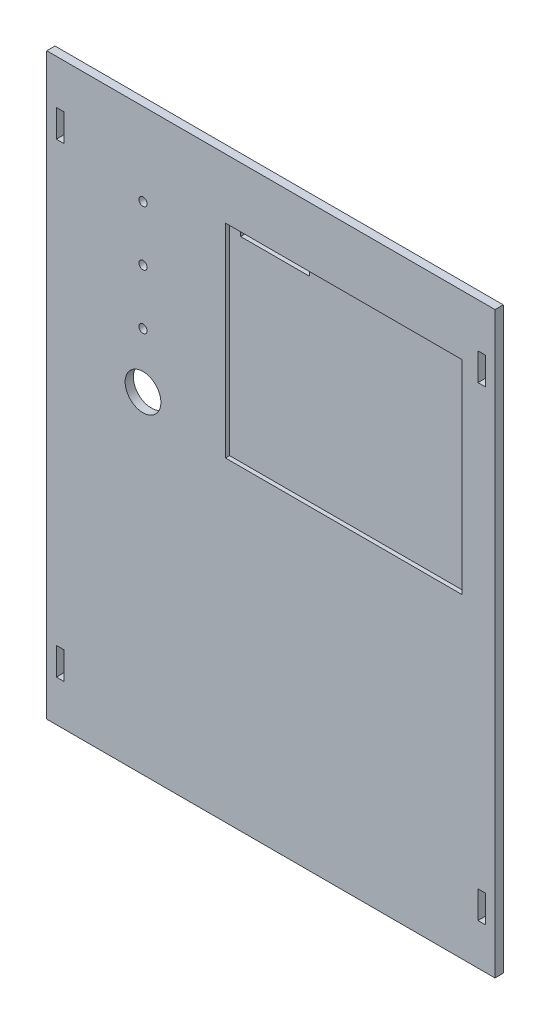
SolidWorks part; units mm, degrees
ref_plane "Front" through (0, 0, 0) normal (0, 0, 1) x (1, 0, 0)
ref_plane "Top" through (0, 0, 0) normal (0, 1, 0) x (1, 0, 0)
ref_plane "Right" through (0, 0, 0) normal (1, 0, 0) x (0, 0, -1)
sketch "Sketch1" plane through (0, 0, 0) normal (0, 0, 1) x (1, 0, 0)
  line L1 (-81.5, 105.25) -> (81.5, 105.25)
  line L2 (-81.5, 105.25) -> (-81.5, -105.25)
  line L3 (-81.5, -105.25) -> (81.5, -105.25)
  line L4 (81.5, 105.25) -> (81.5, -105.25)
  line L5 (-81.5, 105.25) -> (81.5, -105.25) construction
  line L6 (-81.5, -105.25) -> (81.5, 105.25) construction
  point P0 (0, 0)
  dimension "D1" = 163
  dimension "D2" = 210.5
extrude "Boss-Extrude1" add sketch "Sketch1" along normal blind 3 contours L1 L4 L3 L2
sketch "Sketch2" plane through (0, 0, 3) normal (0, 0, 1) x (1, 0, 0)
  line L0 (-81.5, 105.25) -> (81.5, 105.25) construction
  line L1 (-78, -80.25) -> (-75.3, -80.25)
  line L2 (-78, -80.25) -> (-78, -90.25)
  line L3 (-78, -90.25) -> (-75.3, -90.25)
  line L4 (-75.3, -80.25) -> (-75.3, -90.25)
  line L5 (-81.5, 105.25) -> (-81.5, -105.25) construction
  line L6 (-81.5, -105.25) -> (81.5, -105.25) construction
  line L7 (-78, 89.15) -> (-75.3, 89.15)
  line L8 (-78, 89.15) -> (-78, 79.15)
  line L9 (-78, 79.15) -> (-75.3, 79.15)
  line L10 (-75.3, 89.15) -> (-75.3, 79.15)
  dimension "D1" = 10
  dimension "D2" = 2.7
  dimension "D3" = 16.1
  dimension "D4" = 3.5
  dimension "D5" = 10
  dimension "D6" = 3.5
  dimension "D7" = 2.7
  dimension "D8" = 15
extrude "Cut-Extrude1" cut sketch "Sketch2" against normal up to next (3 mm away) contours L4 L3 L2 L1 | L8 L9 L10 L7
mirror "Mirror3" about plane through (0, 0, 0) normal (1, 0, 0) of "Cut-Extrude1"
sketch "Sketch3" plane through (0, 0, 3) normal (0, 0, 1) x (1, 0, 0)
  line L0 (81.5, 105.25) -> (81.5, -105.25) construction
  line L1 (69.5, 83.5) -> (-16.5, 83.5)
  line L2 (69.5, 83.5) -> (69.5, 9.5)
  line L3 (69.5, 9.5) -> (-16.5, 9.5)
  line L4 (-16.5, 83.5) -> (-16.5, 9.5)
  line L5 (-81.5, 105.25) -> (81.5, 105.25) construction
  dimension "D1" = 86
  dimension "D2" = 74
  dimension "D3" = 12
  dimension "D4" = 21.75
extrude "Cut-Extrude2" cut sketch "Sketch3" against normal blind 1.5
sketch "Sketch4" plane through (0, 0, 1.5) normal (0, 0, 1) x (1, 0, 0)
  line L0 (69.5, 83.5) -> (-16.5, 83.5) construction
  line L1 (-12.5, 83.5) -> (12.5, 83.5)
  line L2 (-12.5, 83.5) -> (-12.5, 80.5)
  line L3 (-12.5, 80.5) -> (12.5, 80.5)
  line L4 (12.5, 83.5) -> (12.5, 80.5)
  line L5 (-16.5, 83.5) -> (-16.5, 9.5) construction
  dimension "D1" = 4
  dimension "D2" = 25
  dimension "D3" = 3
extrude "Cut-Extrude3" cut sketch "Sketch4" against normal up to next
sketch "Sketch5" plane through (0, 0, 3) normal (0, 0, 1) x (1, 0, 0)
  line L0 (-81.5, 105.25) -> (81.5, 105.25) construction
  line L1 (-81.5, 105.25) -> (-81.5, -105.25) construction
  circle A0 centre (-46.5, 75.25) radius 1.5
  circle A1 centre (-46.5, 55.25) radius 1.5
  circle A2 centre (-46.5, 35.25) radius 1.5
  circle A3 centre (-46.5, 15.25) radius 6.5
  dimension "D1" = 3
  dimension "D6" = 13
  dimension "D2" = 20
  dimension "D3" = 20
  dimension "D4" = 30
  dimension "D5" = 20
  dimension "D7" = 35
  dimension "D8" = 35
  dimension "D9" = 35
  dimension "D10" = 35
extrude "Cut-Extrude5" cut sketch "Sketch5" against normal up to next
